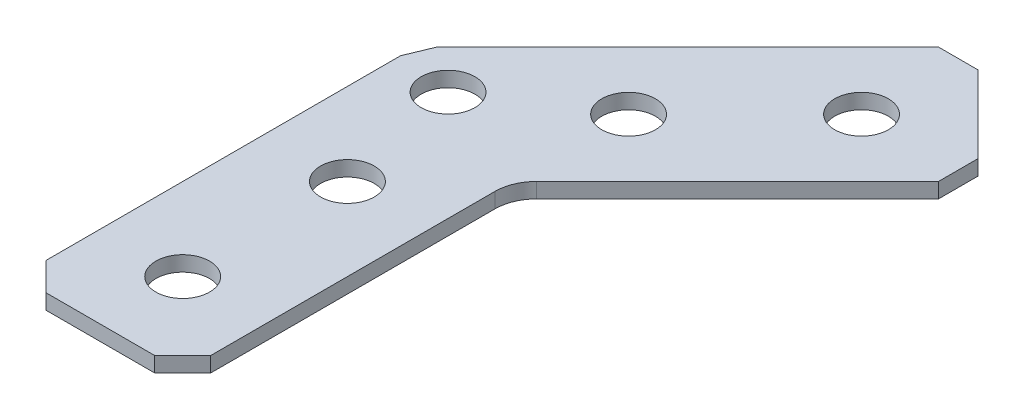
SolidWorks part; units mm, degrees
material "Custom Plastic"
ref_plane "Front Plane" through (0, 0, 0) normal (0, 0, 1) x (1, 0, 0)
ref_plane "Top Plane" through (0, 0, 0) normal (0, 1, 0) x (1, 0, 0)
ref_plane "Right Plane" through (0, 0, 0) normal (1, 0, 0) x (0, 0, -1)
ref_plane "Plane1" through (0, 1.1684, 0) normal (0, 1, 0) x (1, 0, 0)
sketch "Sketch1" plane through (0, 1.1684, 0) normal (0, 1, 0) x (1, 0, 0)
  line L0 (16.8569, 38.1141) -> (13.8036, 38.1141)
  line L1 (13.8036, 38.1141) -> (-5.5238, 18.7867)
  line L2 (-5.5238, 18.7867) -> (-6.35, 16.7921)
  line L3 (-6.35, 16.7921) -> (-6.35, -10.541)
  line L4 (-6.35, -10.541) -> (-4.191, -12.7)
  line L5 (-4.191, -12.7) -> (4.191, -12.7)
  line L6 (4.191, -12.7) -> (6.35, -10.541)
  line L7 (6.35, -10.541) -> (6.35, 11.3849)
  line L8 (7.2799, 13.6299) -> (22.7839, 29.1339)
  line L9 (22.7839, 29.1339) -> (22.7839, 32.1872)
  line L10 (22.7839, 32.1872) -> (16.8569, 38.1141)
  circle A0 centre (15.3303, 30.6605) radius 2.0701
  circle A1 centre (0, 6.35) radius 2.0701
  circle A2 centre (-2.0855, 16.1941) radius 2.0701
  arc A3 (6.35, 11.3849) -> (7.2799, 13.6299) centre (9.525, 11.3849) cw
  circle A4 centre (0, -6.35) radius 2.0701
  circle A5 centre (6.35, 21.6803) radius 2.0701
extrude "Boss-Extrude1" add sketch "Sketch1" against normal blind 1.1684
